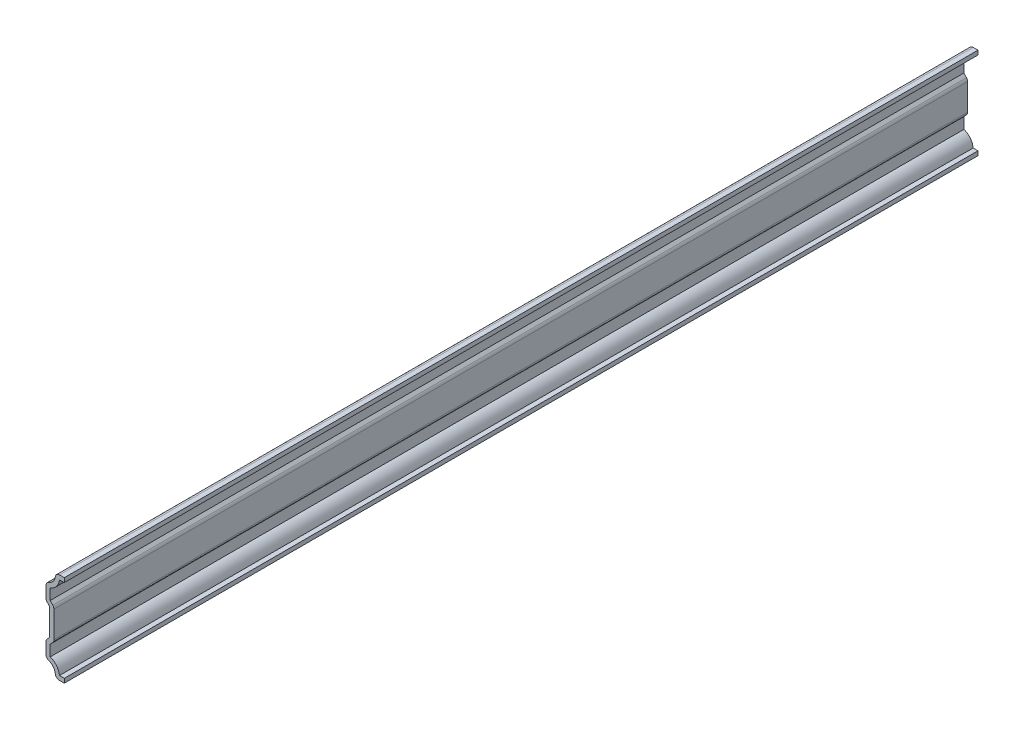
SolidWorks part; units mm, degrees
ref_plane "Front Plane" through (0, 0, 0) normal (0, 0, 1) x (1, 0, 0)
ref_plane "Top Plane" through (0, 0, 0) normal (0, 1, 0) x (1, 0, 0)
ref_plane "Right Plane" through (0, 0, 0) normal (1, 0, 0) x (0, 0, -1)
sketch "Sketch1" plane through (0, 0, 0) normal (0, 0, 1) x (1, 0, 0)
  line L0 (0, 0) -> (0, 35.7188) construction
  line L1 (0, 0) -> (-3.6972, 0)
  line L2 (-7.1437, 4.7625) -> (-7.1437, 11.1125)
  line L3 (-5.715, 12.6683) -> (-5.715, 23.0504)
  line L4 (0, 17.8594) -> (-5.715, 17.8594) construction
  line L5 (-7.1437, 11.1125) -> (-5.715, 12.6683)
  line L6 (1.9565, 0.1894) -> (1.9565, 35.9081) construction
  line L7 (-7.1437, 24.6063) -> (-5.715, 23.0504)
  line L8 (-7.1437, 30.9563) -> (-7.1437, 24.6063)
  line L9 (0, 35.7188) -> (-3.6972, 35.7188)
  arc A0 (-3.6972, 0) -> (-7.1437, 4.7625) centre (-7.1437, 1.1341) ccw
  arc A1 (-3.6972, 35.7188) -> (-7.1437, 30.9563) centre (-7.1437, 34.5846) cw
  point P12 (0, 0)
  point P13 (0, 0)
  point P14 (-4.509, 0)
  point P15 (-3.4159, 0)
  point P16 (-7.1437, 0.969)
  point P17 (-5.9193, 11.5094)
  point P18 (-5.5747, 12.7497)
  point P19 (-5.6527, 17.8594)
  point P25 (-7.1437, 24.6063)
  point P26 (-3.6972, 35.7188)
  dimension "D1" = 35.7188
  dimension "D2" = 4.7625
  dimension "D3" = 6.35
  dimension "D4" = 7.1437
  dimension "D5" = 11.43
  dimension "D6" = 35.7188
extrude "Extrude-Thin1" add sketch "Sketch1" against normal blind 357.1875 thin
fillet "Fillet1" radius 1.651 8 edges at (-3.6972, 0, -178.5938) (-7.1437, 4.7625, -178.5938) (-7.1437, 11.1125, -178.5938) (-4.064, 12.0253, -178.5938) (-4.064, 23.6935, -178.5938) (-7.1437, 24.6063, -178.5938) (-7.1437, 30.9563, -178.5938) (-3.6972, 35.7188, -178.5938)
